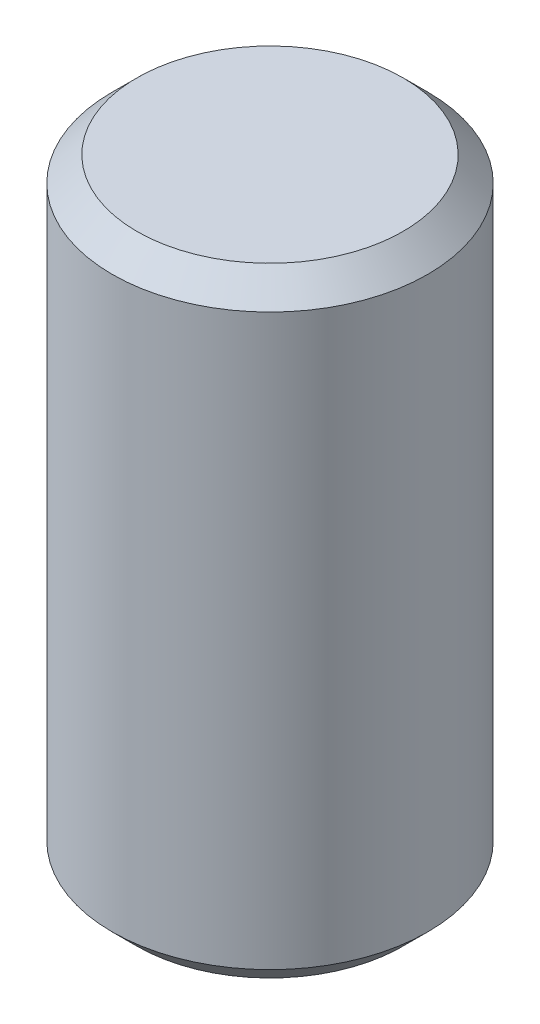
SolidWorks part; units mm, degrees
ref_plane "Front" through (0, 0, 0) normal (0, 0, 1) x (1, 0, 0)
ref_plane "Top" through (0, 0, 0) normal (0, 1, 0) x (1, 0, 0)
ref_plane "Right" through (0, 0, 0) normal (1, 0, 0) x (0, 0, -1)
sketch "Sketch1" plane through (0, 0, 0) normal (0, 0, 1) x (1, 0, 0)
  line L0 (0, 6.0802) -> (0, -6.0802) construction
  line L1 (0, -6.35) -> (3.2385, -6.35)
  line L2 (3.2385, -6.35) -> (3.2385, 6.35)
  line L3 (3.2385, 6.35) -> (0, 6.35)
  line L4 (0, 6.35) -> (0, -6.35)
  point P6 (0, 0)
  dimension "D1" = 6.477
  dimension "D2" = 12.7
revolve "Revolve1" add sketch "Sketch1" angle 360 about L0
chamfer "Chamfer1" distance 0.508 angle 45 2 edges at (0, -6.35, 3.2385) (0, 6.35, 3.2385)
